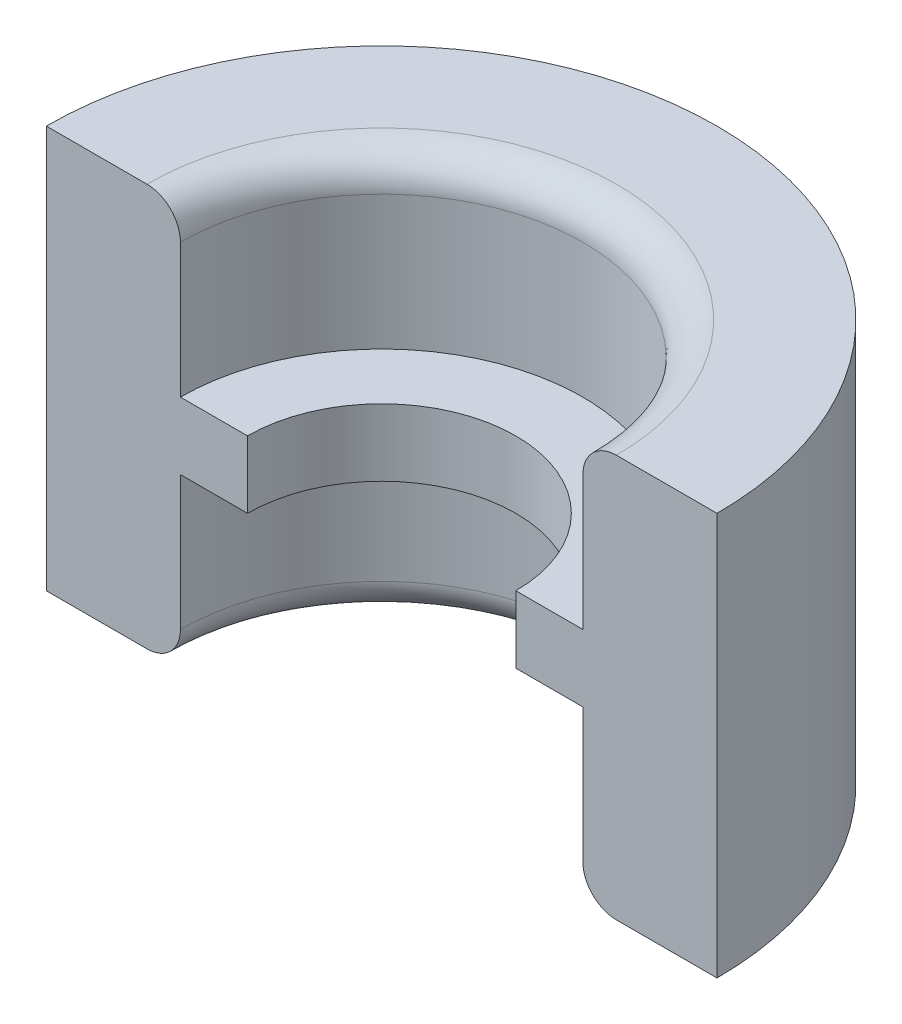
SolidWorks part; units mm, degrees
ref_plane "Front Plane" through (0, 0, 0) normal (0, 0, 1) x (1, 0, 0)
ref_plane "Top Plane" through (0, 0, 0) normal (0, 1, 0) x (1, 0, 0)
ref_plane "Right Plane" through (0, 0, 0) normal (1, 0, 0) x (0, 0, -1)
sketch "Sketch1" plane through (0, 0, 0) normal (0, 0, 1) x (1, 0, 0)
  line L0 (0, 0) -> (0, 2.4253) construction
  line L1 (0, 2.4253) -> (0, -2.7565) construction
  line L3 (2.5, 0) -> (3.5, 0) construction
  line L4 (3, 3) -> (5, 3)
  line L5 (3, 3) -> (3, -3)
  line L6 (3, -3) -> (5, -3)
  line L7 (5, 3) -> (5, -3)
  line L8 (2, 0.5) -> (3, 0.5)
  line L9 (2, 0.5) -> (2, -0.5)
  line L10 (2, -0.5) -> (3, -0.5)
  line L11 (3, 0.5) -> (3, -0.5)
  line L12 (2, 0.5) -> (3, -0.5) construction
  line L13 (2, -0.5) -> (3, 0.5) construction
  point P11 (3, 0)
  dimension "D1" = 1
  dimension "D2" = 2
  dimension "D3" = 6
  dimension "D4" = 1
revolve "Revolve2" add sketch "Sketch1" angle 180 about L0
fillet "Fillet3" radius 0.5 2 edges at (0, 3, -3) (0, -3, -3)
